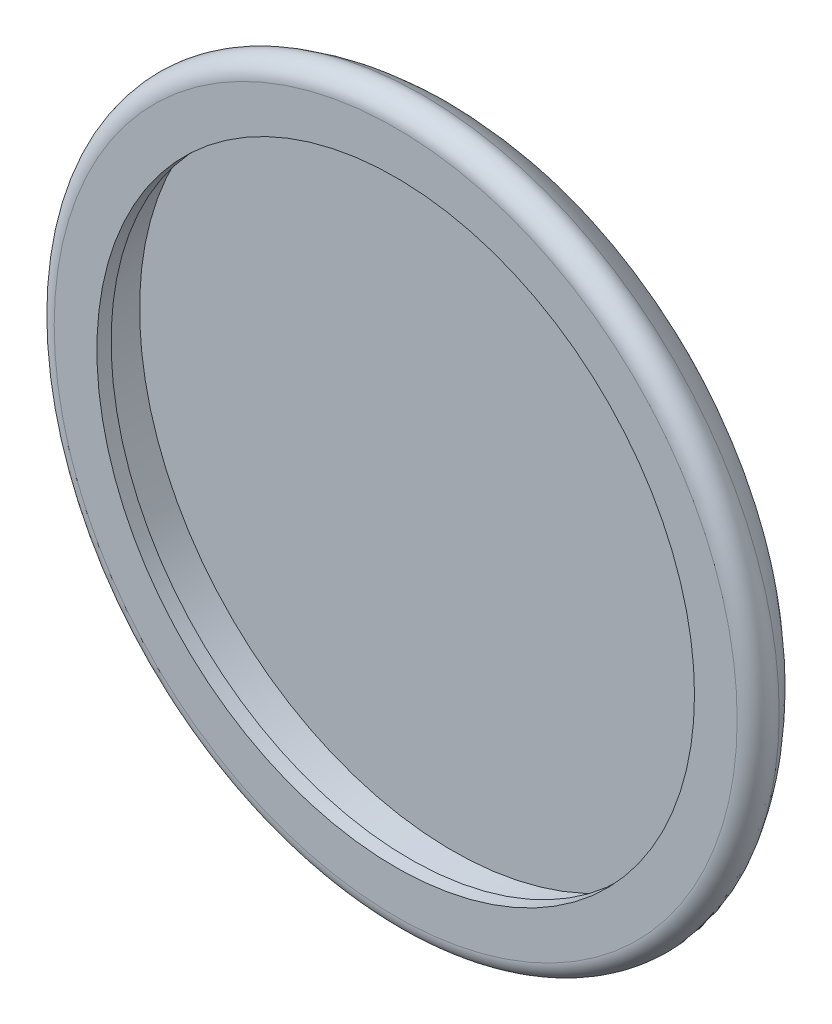
SolidWorks part; units mm, degrees
ref_plane "Front Plane" through (0, 0, 0) normal (0, 0, 1) x (1, 0, 0)
ref_plane "Top Plane" through (0, 0, 0) normal (0, 1, 0) x (1, 0, 0)
ref_plane "Right Plane" through (0, 0, 0) normal (1, 0, 0) x (0, 0, -1)
sketch "Croquis1" plane through (0, 0, 0) normal (0, 1, 0) x (1, 0, 0)
  line L0 (0, 0) -> (0, 10.5709) construction
  line L1 (0, 6) -> (18, 6)
  line L2 (24, 0) -> (21, 0)
  line L3 (0, 4) -> (22, 4)
  line L5 (0, 6) -> (0, 4)
  line L6 (21, 0) -> (21, 1)
  line L7 (21, 1) -> (22, 1)
  line L8 (22, 1) -> (22, 4)
  arc A0 (18, 6) -> (25.0881, 1.8653) centre (18, -2.1429) cw
  arc A1 (25.0881, 1.8653) -> (24, 0) centre (24, 1.25) cw
  dimension "D3" = 24
  dimension "D4" = 6
  dimension "D5" = 22
  dimension "D7" = 1.25
  dimension "D1" = 18
  dimension "D2" = 4
  dimension "D6" = 21
  dimension "D8" = 1
revolve "Revolución1" add sketch "Croquis1" angle 360 about L0
